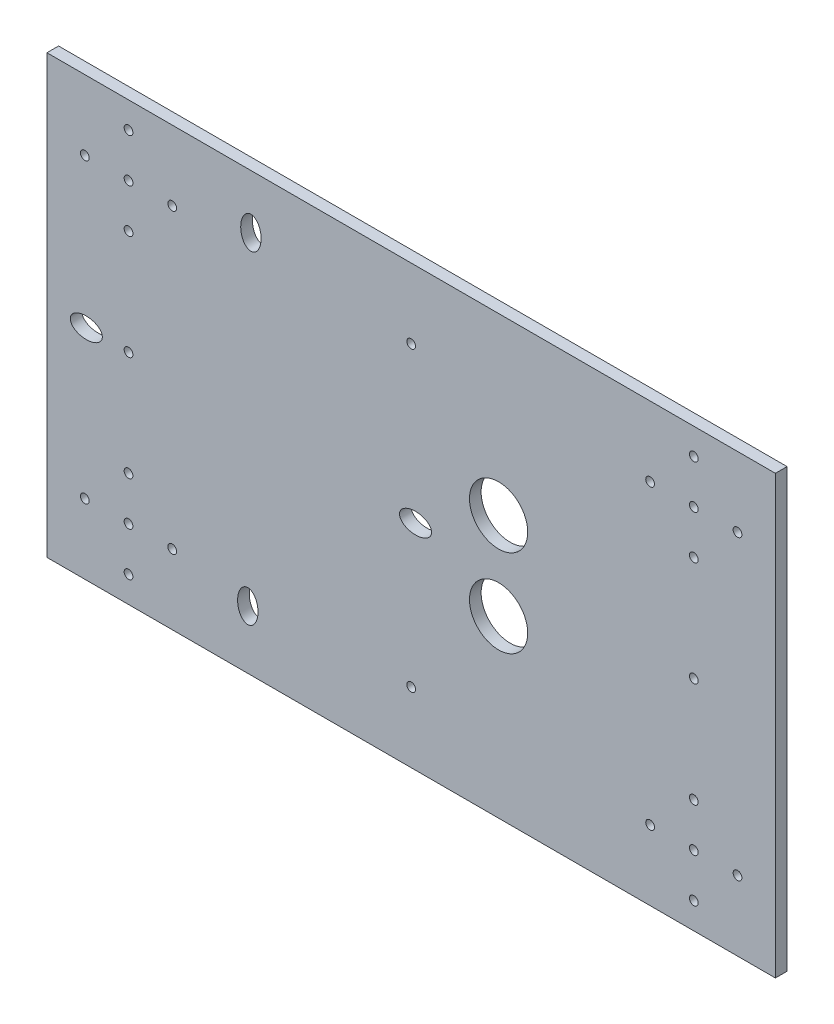
SolidWorks part; units mm, degrees
ref_plane "Front Plane" through (0, 0, 0) normal (0, 0, 1) x (1, 0, 0)
ref_plane "Top Plane" through (0, 0, 0) normal (0, 1, 0) x (1, 0, 0)
ref_plane "Right Plane" through (0, 0, 0) normal (1, 0, 0) x (0, 0, -1)
sketch "Sketch1" plane through (0, 0, 0) normal (0, 0, 1) x (1, 0, 0)
  line L1 (-60.0985, 33.8667) -> (189.9015, 33.8667)
  line L2 (-60.0985, 33.8667) -> (-60.0985, -116.1333)
  line L3 (-60.0985, -116.1333) -> (189.9015, -116.1333)
  line L4 (189.9015, 33.8667) -> (189.9015, -116.1333)
  circle A0 centre (-32.0985, -92.1333) radius 1.5
  circle A1 centre (-17.0985, -92.1333) radius 1.5
  circle A2 centre (-32.0985, -107.1333) radius 1.5
  circle A3 centre (-47.0985, -92.1333) radius 1.5
  circle A4 centre (-32.0985, -77.1333) radius 1.5
  circle A5 centre (176.9015, -92.1333) radius 1.5
  circle A6 centre (161.9015, -92.1333) radius 1.5
  circle A7 centre (161.9015, -77.1333) radius 1.5
  circle A8 centre (146.9015, -92.1333) radius 1.5
  circle A9 centre (161.9015, -107.1333) radius 1.5
  circle A10 centre (176.9015, 9.8667) radius 1.5
  circle A11 centre (161.9015, 9.8667) radius 1.5
  circle A12 centre (161.9015, 24.8667) radius 1.5
  circle A13 centre (146.9015, 9.8667) radius 1.5
  circle A14 centre (161.9015, -5.1333) radius 1.5
  circle A15 centre (-17.0985, 9.8667) radius 1.5
  circle A16 centre (-32.0985, 9.8667) radius 1.5
  circle A17 centre (-32.0985, 24.8667) radius 1.5
  circle A18 centre (-47.0985, 9.8667) radius 1.5
  circle A19 centre (-32.0985, -5.1333) radius 1.5
  circle A20 centre (-32.0985, -41.1333) radius 1.5
  circle A21 centre (161.9015, -41.1333) radius 1.5
  circle A22 centre (64.9015, 9.8667) radius 1.5
  circle A23 centre (64.9015, -92.1333) radius 1.5
  circle A24 centre (94.9015, -26.1333) radius 10
  circle A25 centre (94.9015, -56.1333) radius 10
  ellipse E0 centre (-46.5985, -41.1333) end of major axis (-41.0985, -41.1333) minor radius 3.5
  ellipse E1 centre (9.9015, 15.3667) end of major axis (9.9015, 9.8667) minor radius 3.5
  ellipse E2 centre (66.4015, -42.6994) end of major axis (60.9015, -42.6994) minor radius 3.5
  ellipse E3 centre (8.8354, -96.1333) end of major axis (8.8354, -101.6333) minor radius 3.5
  point P28 (-32.0985, -92.1333)
  point P84 (9.9015, -41.1333)
  dimension "D1" = 2
  dimension "D2" = 2
  dimension "D3" = 24
  dimension "D4" = 60
  dimension "D5" = 15
  dimension "D7" = 2
  dimension "D9" = 2
  dimension "D8" = 2
  dimension "D6" = 4
extrude "Boss-Extrude3" add sketch "Sketch1" along normal blind 4
